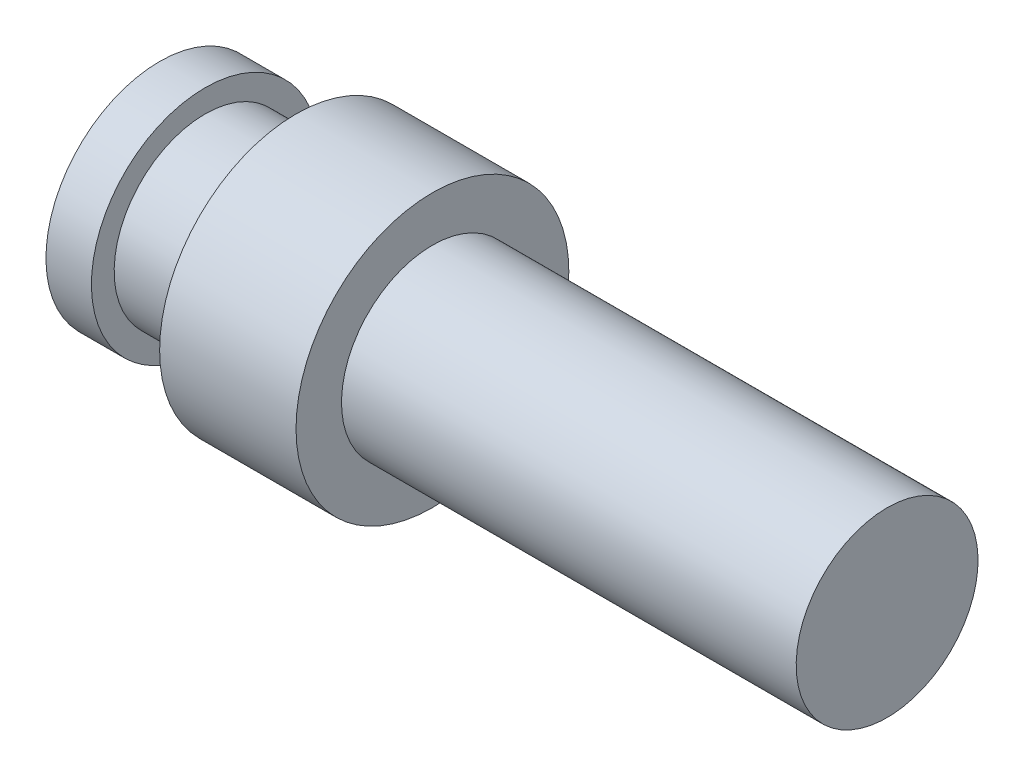
SolidWorks part; units mm, degrees
ref_plane "Face" through (0, 0, 0) normal (0, 0, 1) x (1, 0, 0)
ref_plane "Dessus" through (0, 0, 0) normal (0, 1, 0) x (1, 0, 0)
ref_plane "Droite" through (0, 0, 0) normal (1, 0, 0) x (0, 0, -1)
sketch "Esquisse1" plane through (0, 0, 0) normal (0, 0, 1) x (1, 0, 0)
  line L0 (0, 0) -> (0, 2.5)
  line L1 (0, 2.5) -> (1, 2.5)
  line L2 (1, 2.5) -> (1, 2)
  line L3 (3, 2) -> (3, 3)
  line L4 (3, 3) -> (6, 3)
  line L5 (16, 2) -> (16, 0)
  line L6 (16, 0) -> (0, 0)
  line L7 (1, 2) -> (3, 2)
  line L8 (6, 3) -> (6, 2)
  line L9 (6, 2) -> (16, 2)
  dimension "D1" = 2.5
  dimension "D2" = 1
  dimension "D3" = 2
  dimension "D4" = 2
  dimension "D5" = 3
  dimension "D6" = 16
  dimension "D7" = 2
  dimension "D8" = 10
revolve "Révolution1" add sketch "Esquisse1" angle 360 about L6
